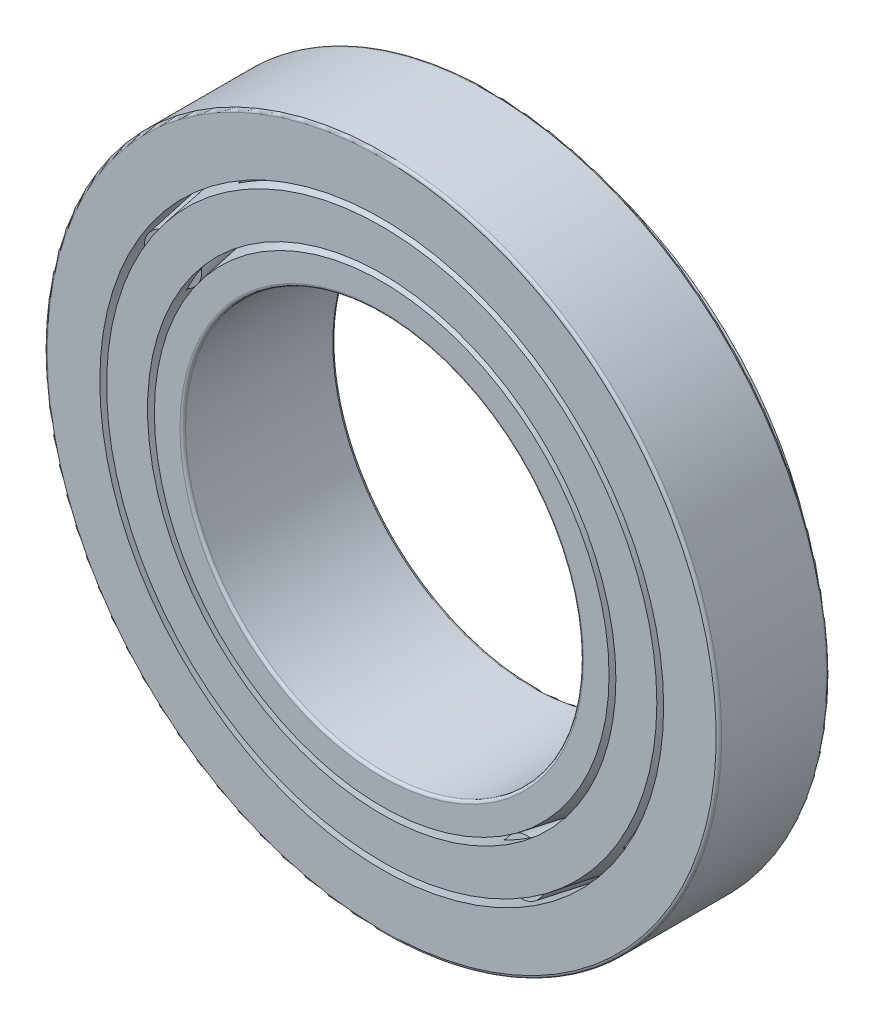
SolidWorks part; units mm, degrees
material "Cast Alloy Steel"
ref_plane "Front Plane" through (0, 0, 0) normal (0, 0, 1) x (1, 0, 0)
ref_plane "Top Plane" through (0, 0, 0) normal (0, 1, 0) x (1, 0, 0)
ref_plane "Right Plane" through (0, 0, 0) normal (1, 0, 0) x (0, 0, -1)
sketch "Sketch1" plane through (0, 0, 0) normal (1, 0, 0) x (0, 0, -1)
  line L0 (-10.9728, 0) -> (10.9728, 0) construction
  line L1 (0, 0) -> (0, 48.4187) construction
  line L2 (-10.9728, 28.575) -> (10.9728, 28.575) construction
  line L3 (10.9728, 28.575) -> (10.9728, 36.5125) construction
  line L4 (10.9728, 36.5125) -> (-10.9728, 32.6429) construction
  line L5 (-10.9728, 32.6429) -> (-10.9728, 28.575) construction
  line L7 (-10.9728, 48.4187) -> (4.9022, 48.4187)
  line L8 (4.9022, 48.4187) -> (4.9022, 43.2804)
  line L9 (4.9022, 43.2804) -> (-10.9728, 40.4812)
  line L10 (-10.9728, 40.4812) -> (-10.9728, 48.4187)
  line L11 (-10.9728, 40.4812) -> (-9.6324, 32.8793) construction
  line L12 (8.6875, 43.9479) -> (10.0279, 36.3459) construction
  line L14 (-10.9728, 32.6429) -> (-9.6324, 32.8793) construction
  line L15 (-10.9728, 32.6429) -> (10.0279, 36.3459) construction
  point P5 (0, 28.575)
  dimension "D1" = 100
  dimension "Width" = 21.9456
  dimension "OD" = 96.8375
  dimension "Shaft Dia" = 57.15
  dimension "D2" = 19.8438
  dimension "D3" = 7.9375
  dimension "Outer Wd" = 15.875
  dimension "Bearing Wd" = 21.0007
revolve "Revolve1" add sketch "Sketch1" angle 360 about L0
sketch "Sketch5" plane through (0, 0, 0) normal (1, 0, 0) x (0, 0, -1)
  line L0 (10.9728, 36.5125) -> (-10.9728, 32.6429) construction
  line L1 (10.9728, 36.5125) -> (-10.9728, 32.6429)
  line L2 (-10.9728, 32.6429) -> (-10.9728, 28.575)
  line L3 (-10.9728, 28.575) -> (10.9728, 28.575)
  line L4 (10.9728, 28.575) -> (10.9728, 36.5125)
revolve "Revolve4" add sketch "Sketch5" angle 360 about L0
sketch "Sketch2" plane through (0, 0, 0) normal (1, 0, 0) x (0, 0, -1)
  line L0 (-10.9728, 39.5015) -> (-10.9728, 33.6227)
  line L1 (4.9022, 42.3006) -> (8.855, 42.9976)
  line L2 (-10.9728, 33.6227) -> (4.9022, 36.4219)
  line L3 (8.6875, 43.9479) -> (10.0279, 36.3459) construction
  line L4 (4.9022, 36.4219) -> (4.9022, 42.3006) construction
  line L5 (4.9022, 42.3006) -> (-10.9728, 39.5015)
  line L6 (4.9022, 43.2804) -> (-10.9728, 40.4812) construction
  line L7 (10.9728, 36.5125) -> (-10.9728, 32.6429) construction
  line L8 (-10.9728, 40.4812) -> (4.9022, 43.2804) construction
  line L9 (-10.9728, 32.6429) -> (10.0279, 36.3459) construction
  line L10 (8.855, 42.9976) -> (9.8604, 37.2961)
  line L11 (-10.9728, 40.4812) -> (-10.9728, 39.5015) construction
  line L12 (-10.9728, 33.6227) -> (-10.9728, 32.6429) construction
  line L13 (4.9022, 48.4187) -> (4.9022, 43.2804) construction
  line L14 (9.8604, 37.2961) -> (4.9022, 36.4219)
  dimension "D1" = 7.7193
  dimension "D2" = 5.7895
revolve "Revolve2" add sketch "Sketch2" angle 360 about L0
sketch "Sketch3" plane through (0, 0, 0) normal (1, 0, 0) x (0, 0, -1)
  line L0 (-10.9728, 36.5621) -> (4.9022, 39.3613) construction
  line L1 (-10.9728, 39.5015) -> (-10.9728, 33.6227) construction
  line L2 (4.9022, 36.4219) -> (4.9022, 42.3006) construction
  line L3 (-8.9621, 36.9166) -> (-9.6324, 40.7176)
  line L5 (-9.6324, 40.7176) -> (4.232, 43.1623)
  line L6 (4.232, 43.1623) -> (4.9022, 39.3613)
  line L7 (4.9022, 39.3613) -> (-8.9621, 36.9166)
  line L8 (4.9022, 43.2804) -> (-10.9728, 40.4812) construction
  line L9 (-10.9728, 36.5621) -> (-10.3026, 36.6803) construction
  line L10 (-10.9728, 40.4812) -> (-9.6324, 32.8793) construction
  line L11 (-10.3026, 36.6803) -> (-9.6324, 36.7984) construction
  line L12 (-9.6324, 36.7984) -> (-8.9621, 36.9166) construction
revolve "Cut-Revolve1" cut sketch "Sketch3" angle 360 about L0
sketch "Sketch4" plane through (0, 0, 0) normal (1, 0, 0) x (0, 0, -1)
  line L0 (-9.5883, 40.4675) -> (4.2761, 42.9121)
  line L1 (4.2761, 42.9121) -> (4.9022, 39.3613)
  line L2 (4.9022, 39.3613) -> (-8.9621, 36.9166)
  line L3 (-10.9728, 36.5621) -> (-8.9621, 36.9166) construction
  line L4 (-8.9621, 36.9166) -> (-9.5883, 40.4675)
  line L6 (4.9022, 39.3613) -> (-8.9621, 36.9166) construction
  line L7 (4.9022, 43.2804) -> (-10.9728, 40.4812) construction
  dimension "D1" = 0.254
revolve "Revolve3" add sketch "Sketch4" angle 360 about L0
ref_axis "Axis1" through (0, 0, -10.9728) along (0, 0, 1)
pattern_circular "CirPattern1" count 12 every 30 about axis through (0, 0, 0) along (0, 0, 1) of "Cut-Revolve1"
pattern_circular "CirPattern2" count 12 every 30 about axis through (0, 0, -10.9728) along (0, 0, 1) of bodies 403
fillet "Fillet1" radius 0.3969 2 edges at (48.4187, 0, -4.9022) (48.4187, 0, 10.9728)
fillet "Fillet2" radius 0.3969 2 edges at (28.575, 0, -10.9728) (28.575, 0, 10.9728)
sketch "Sketch6" plane through (0, 0, 0) normal (1, 0, 0) x (0, 0, -1)
  line L0 (-77.6478, 48.4187) -> (-77.6478, 40.4812)
  line L1 (-77.6478, 40.4812) -> (-61.7728, 43.2804)
  line L2 (-61.7728, 43.2804) -> (-61.7728, 48.4187)
  line L3 (-61.7728, 48.4187) -> (-77.6478, 48.4187)
  line L4 (-10.9728, 48.4187) -> (4.9022, 48.4187) construction
  line L5 (-10.9728, 40.4812) -> (-10.9728, 48.4187) construction
  line L6 (4.9022, 48.4187) -> (4.9022, 43.2804) construction
  line L8 (-10.9728, 48.0219) -> (-10.9728, -48.0219) construction
  dimension "D1" = 50.8
revolve "Revolve5" [suppressed] add sketch "Sketch6" angle 360 about L0
fillet "Fillet3" [suppressed] radius 0.3969
delete or keep bodies "Body-Delete1" [suppressed] type delete bodies bodies 399
equation "\"D3@Sketch1\" = \"D2@Sketch1\"/2.5"
equation "\"D2@Sketch2\" = \"D1@Sketch2\"*.75"
equation "\"Rollers@CirPattern2\" = \"OD@Sketch1\"*3.0625"
equation "\"Angle@CirPattern2\" = 360/\"Rollers@CirPattern2\""
equation "\"D1@CirPattern1\" = \"Rollers@CirPattern2\""
equation "\"D2@CirPattern1\" = \"Angle@CirPattern2\""
equation "\"D1@Fillet1\" = \"Outer Wd@Sketch1\"*.025"
equation "\"D1@Fillet2\" = \"D1@Fillet1\""
equation "\"D1@Fillet3\" = \"D1@Fillet1\""
